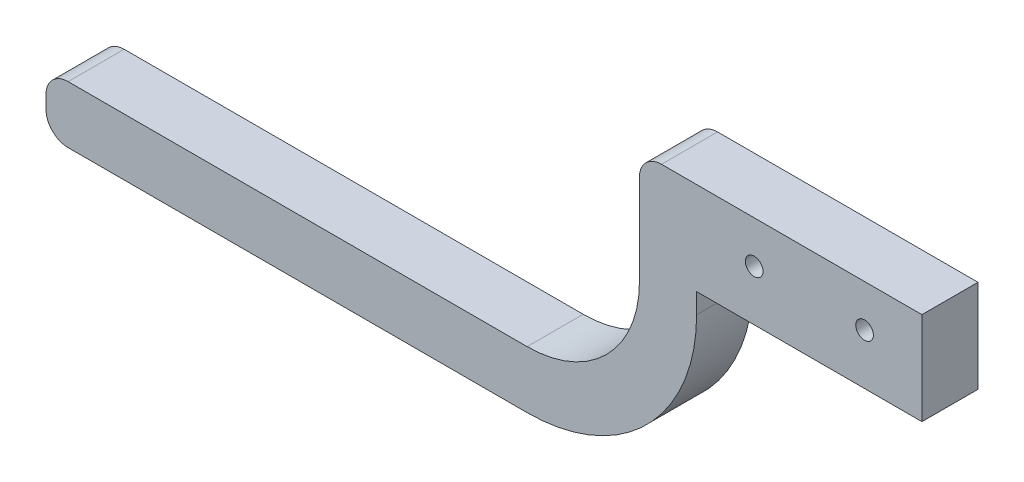
SolidWorks part; units mm, degrees
ref_plane "Front Plane" through (0, 0, 0) normal (0, 0, 1) x (1, 0, 0)
ref_plane "Top Plane" through (0, 0, 0) normal (0, 1, 0) x (1, 0, 0)
ref_plane "Right Plane" through (0, 0, 0) normal (1, 0, 0) x (0, 0, -1)
sketch "Sketch1" plane through (0, 0, 0) normal (0, 0, 1) x (1, 0, 0)
  line L0 (0, 0) -> (-64, 0)
  line L1 (-64, 0) -> (-64, -25.5522)
  line L2 (0, 0) -> (0, -21)
  line L3 (0, -21) -> (-51.0441, -21)
  line L4 (-89.4478, -51) -> (-198.4478, -51)
  line L5 (-198.4478, -51) -> (-198.4478, -63.9559)
  line L6 (-198.4478, -63.9559) -> (-89.4478, -63.9559)
  line L7 (-51.0441, -25.5522) -> (-51.0441, -21)
  arc A0 (-64, -25.5522) -> (-89.4478, -51) centre (-89.4478, -25.5522) cw
  arc A2 (-89.4478, -63.9559) -> (-51.0441, -25.5522) centre (-89.4478, -25.5522) ccw
  point P12 (-50.9694, -21)
  dimension "D4" = 4.5522
  dimension "D1" = 64
  dimension "D2" = 21
  dimension "D3" = 30
  dimension "D5" = 109
extrude "Boss-Extrude1" add sketch "Sketch1" along normal blind 12.7
fillet "Fillet1" radius 5 3 edges at (-64, 0, 6.35) (-198.4478, -63.9559, 6.35) (-198.4478, -51, 6.35)
sketch "Sketch2" plane through (0, 0, 12.7) normal (0, 0, 1) x (1, 0, 0)
  line L0 (0, -21) -> (0, 0) construction
  circle A0 centre (-13, -9.5316) radius 2
  circle A1 centre (-38, -9.5316) radius 2
  dimension "D1" = 4
  dimension "D2" = 4
  dimension "D3" = 13
  dimension "D4" = 25
extrude "Cut-Extrude1" cut sketch "Sketch2" against normal through all
